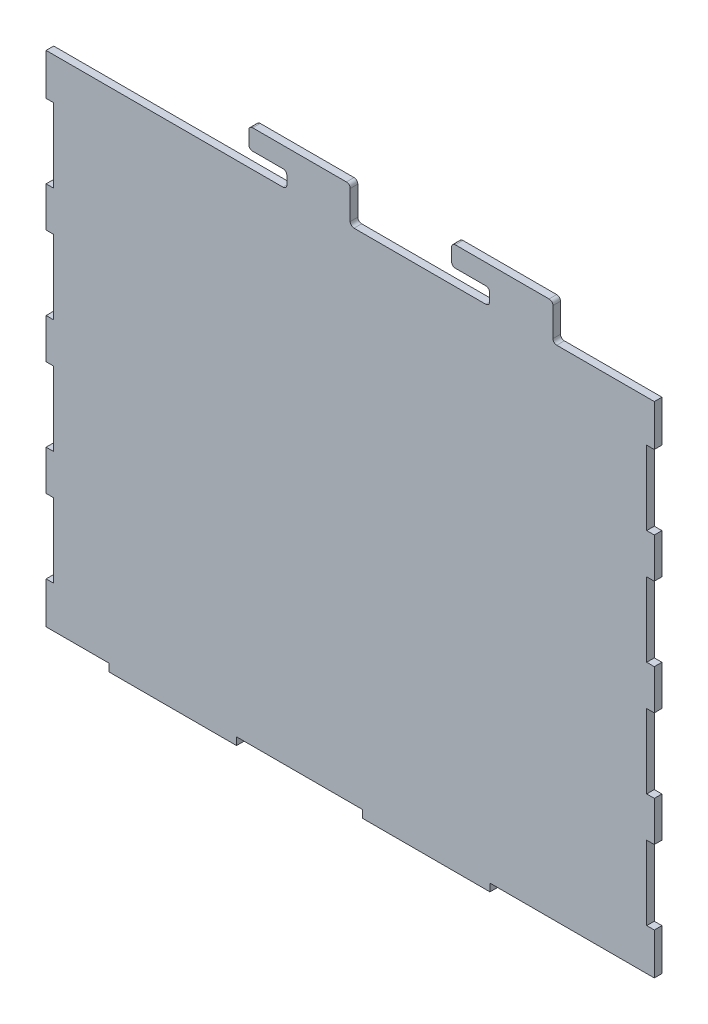
SolidWorks part; units mm, degrees
ref_plane "Alzado" through (0, 0, 0) normal (0, 0, 1) x (1, 0, 0)
ref_plane "Planta" through (0, 0, 0) normal (0, 1, 0) x (1, 0, 0)
ref_plane "Vista lateral" through (0, 0, 0) normal (1, 0, 0) x (0, 0, -1)
sketch "Croquis1" plane through (0, 0, 0) normal (0, 0, 1) x (1, 0, 0)
  line L1 (-120, 100) -> (120, 100)
  line L2 (-120, 100) -> (-120, -100)
  line L3 (-120, -100) -> (120, -100)
  line L4 (120, 100) -> (120, -100)
  line L5 (-120, 100) -> (120, -100) construction
  line L6 (-120, -100) -> (120, 100) construction
  point P0 (0, 0)
  dimension "D1" = 240
  dimension "D2" = 200
extrude "Saliente-Extruir1" add sketch "Croquis1" along normal blind 3
sketch "Croquis2" plane through (0, 0, 0) normal (0, 0, -1) x (-1, 0, 0)
  line L2 (120, 100) -> (120, -100) construction
  line L3 (0, 0) -> (0, 119.5652) construction
  line L6 (-117, -51.4) -> (-117, -80.6)
  line L12 (-117, -51.4) -> (-120, -51.4)
  line L13 (-120, -51.4) -> (-120, -80.6)
  line L14 (-117, -80.6) -> (-120, -80.6)
  line L15 (-117, -6.4) -> (-117, -35.6)
  line L16 (-117, -35.6) -> (-120, -35.6)
  line L17 (-120, -6.4) -> (-120, -35.6)
  line L18 (-117, -6.4) -> (-120, -6.4)
  line L19 (-117, 38.6) -> (-117, 9.4)
  line L20 (-117, 9.4) -> (-120, 9.4)
  line L21 (-120, 38.6) -> (-120, 9.4)
  line L22 (-117, 38.6) -> (-120, 38.6)
  line L23 (-117, 83.6) -> (-117, 54.4)
  line L24 (-117, 54.4) -> (-120, 54.4)
  line L25 (-117, 83.6) -> (-120, 83.6)
  line L26 (-120, 83.6) -> (-120, 54.4)
  line L27 (120, -97) -> (120, -100)
  line L28 (120, -100) -> (95.15, -100)
  line L29 (44.85, -100) -> (-4.85, -100)
  line L30 (-55.15, -100) -> (-121.9346, -100)
  line L129 (95.15, -100) -> (95.15, -97)
  line L130 (95.15, -97) -> (120, -97)
  line L181 (-121.9346, -100) -> (-121.9346, -97)
  line L182 (-121.9346, -97) -> (-55.15, -97)
  line L183 (-55.15, -97) -> (-55.15, -100)
  line L185 (-4.85, -100) -> (-4.85, -97)
  line L186 (-4.85, -97) -> (44.85, -97)
  line L187 (44.85, -97) -> (44.85, -100)
  line L1827 (117, -80.6) -> (120, -80.6)
  line L1828 (120, -51.4) -> (120, -80.6)
  line L1829 (117, -51.4) -> (120, -51.4)
  line L1830 (117, -51.4) -> (117, -80.6)
  line L1831 (117, -6.4) -> (120, -6.4)
  line L1832 (120, -6.4) -> (120, -35.6)
  line L1833 (117, -35.6) -> (120, -35.6)
  line L1834 (117, -6.4) -> (117, -35.6)
  line L1835 (117, 38.6) -> (120, 38.6)
  line L1836 (120, 38.6) -> (120, 9.4)
  line L1837 (117, 9.4) -> (120, 9.4)
  line L1838 (117, 38.6) -> (117, 9.4)
  line L1839 (117, 83.6) -> (120, 83.6)
  line L1840 (120, 83.6) -> (120, 54.4)
  line L1841 (117, 54.4) -> (120, 54.4)
  line L1842 (117, 83.6) -> (117, 54.4)
  dimension "D3" = 3
  dimension "D4" = 50.3
  dimension "D5" = 16.4
  dimension "D6" = 29.2
  dimension "D8" = 15.8
  dimension "D2" = 24.85
  dimension "D7" = 3
  dimension "D9" = 29.2
  dimension "D10" = 15.8
  dimension "D11" = 29.2
  dimension "D12" = 29.2
  dimension "D13" = 15.8
extrude "Cortar-Extruir1" cut sketch "Croquis2" against normal through all
sketch "Croquis3" plane through (0, 0, 0) normal (0, 0, -1) x (-1, 0, 0)
  line L0 (-55, 100) -> (-55, 104.8)
  line L2 (-53.5, 106.3) -> (-41.5, 106.3)
  line L3 (-40, 107.8) -> (-40, 112.8)
  line L4 (-41.5, 114.3) -> (-78.5, 114.3)
  line L5 (-80, 112.8) -> (-80, 100)
  line L6 (-80, 100) -> (-55, 100)
  line L7 (0, 100) -> (25, 100)
  line L8 (25, 100) -> (25, 104.8)
  line L9 (26.5, 106.3) -> (38.5, 106.3)
  line L10 (40, 107.8) -> (40, 112.8)
  line L11 (38.5, 114.3) -> (1.5, 114.3)
  line L12 (0, 112.8) -> (0, 100)
  line L43 (-120, 83.6) -> (-120, 100) construction
  arc A0 (-40, 112.8) -> (-41.5, 114.3) centre (-41.5, 112.8) ccw
  arc A1 (-41.5, 106.3) -> (-40, 107.8) centre (-41.5, 107.8) ccw
  arc A2 (-55, 104.8) -> (-53.5, 106.3) centre (-53.5, 104.8) cw
  arc A3 (-78.5, 114.3) -> (-80, 112.8) centre (-78.5, 112.8) ccw
  arc A24 (25, 104.8) -> (26.5, 106.3) centre (26.5, 104.8) cw
  arc A25 (38.5, 106.3) -> (40, 107.8) centre (38.5, 107.8) ccw
  arc A26 (40, 112.8) -> (38.5, 114.3) centre (38.5, 112.8) ccw
  arc A27 (1.5, 114.3) -> (0, 112.8) centre (1.5, 112.8) ccw
  point P47 (-40, 114.3)
  point P50 (-40, 106.3)
  point P53 (-55, 106.3)
  point P56 (-80, 114.3)
  point P105 (0, 114.3)
  dimension "D8" = 1.5
  dimension "D1" = 25
  dimension "D2" = 40
  dimension "D3" = 6.3
  dimension "D4" = 8
  dimension "D5" = 40
  dimension "D7" = 80
extrude "Saliente-Extruir2" add sketch "Croquis3" against normal blind 3
fillet "Redondeo1" radius 1.5 4 edges at (0, 100, 1.5) (-25, 100, 1.5) (55, 100, 1.5) (80, 100, 1.5)
